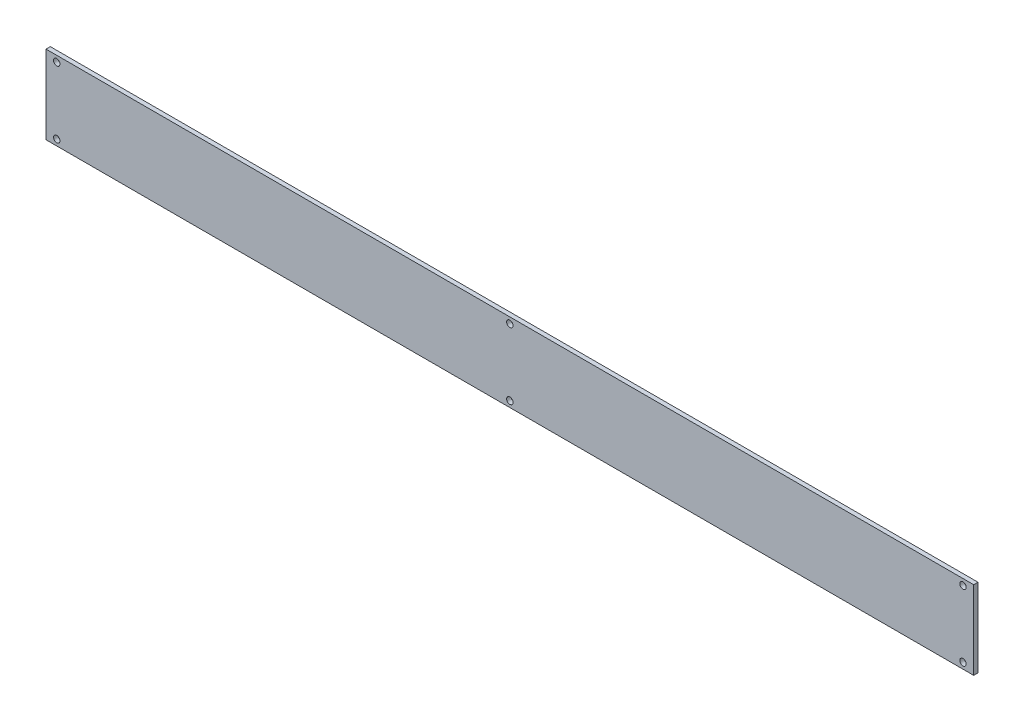
SolidWorks part; units mm, degrees
ref_plane "Front Plane" through (0, 0, 0) normal (0, 0, 1) x (1, 0, 0)
ref_plane "Top Plane" through (0, 0, 0) normal (0, 1, 0) x (1, 0, 0)
ref_plane "Right Plane" through (0, 0, 0) normal (1, 0, 0) x (0, 0, -1)
sketch "Sketch1" plane through (0, 0, 0) normal (0, 0, 1) x (1, 0, 0)
  line L0 (-8.6311, 8.9019) -> (-251.053, 8.9019)
  line L1 (-224.6711, 18.0469) -> (-8.6311, 18.0469)
  line L2 (-224.6711, 18.0469) -> (-224.6711, -0.2431)
  line L3 (-224.6711, -0.2431) -> (-8.6311, -0.2431)
  line L4 (-8.6311, 18.0469) -> (-8.6311, -0.2431)
  line L5 (-224.6711, 18.0469) -> (-8.6311, 18.0469)
  line L6 (-224.6711, 18.0469) -> (-224.6711, 15.2569)
  line L7 (-224.6711, 15.2569) -> (-8.6311, 15.2569)
  line L8 (-8.6311, 18.0469) -> (-8.6311, 15.2569)
  line L9 (-224.6711, -0.2431) -> (-8.6311, -0.2431)
  line L10 (-224.6711, -0.2431) -> (-224.6711, 2.5469)
  line L11 (-224.6711, 2.5469) -> (-8.6311, 2.5469)
  line L12 (-8.6311, -0.2431) -> (-8.6311, 2.5469)
  circle A0 centre (-222.1711, 16.6519) radius 0.75
  circle A1 centre (-116.6511, 16.6519) radius 0.75
  circle A2 centre (-11.1311, 16.6519) radius 0.75
  circle A3 centre (-11.1311, 1.1519) radius 0.75
  circle A4 centre (-116.6511, 1.1519) radius 0.75
  circle A5 centre (-222.1711, 1.1519) radius 0.75
  dimension "D5" = 1.5
  dimension "D7" = 1.5
  dimension "D8" = 1.5
  dimension "D1" = 216.04
  dimension "D2" = 18.29
  dimension "D3" = 2.79
  dimension "D4" = 2.79
  dimension "D6" = 2.5
  dimension "D9" = 2.5
extrude "Boss-Extrude1" add sketch "Sketch1" along normal blind 1 contours L7 L2 L0 L4 | L2 L7 L4 L1 A2 A1 A0 | L2 L11 L4 L0 | L11 L2 L3 L4 A4 A3 A5
